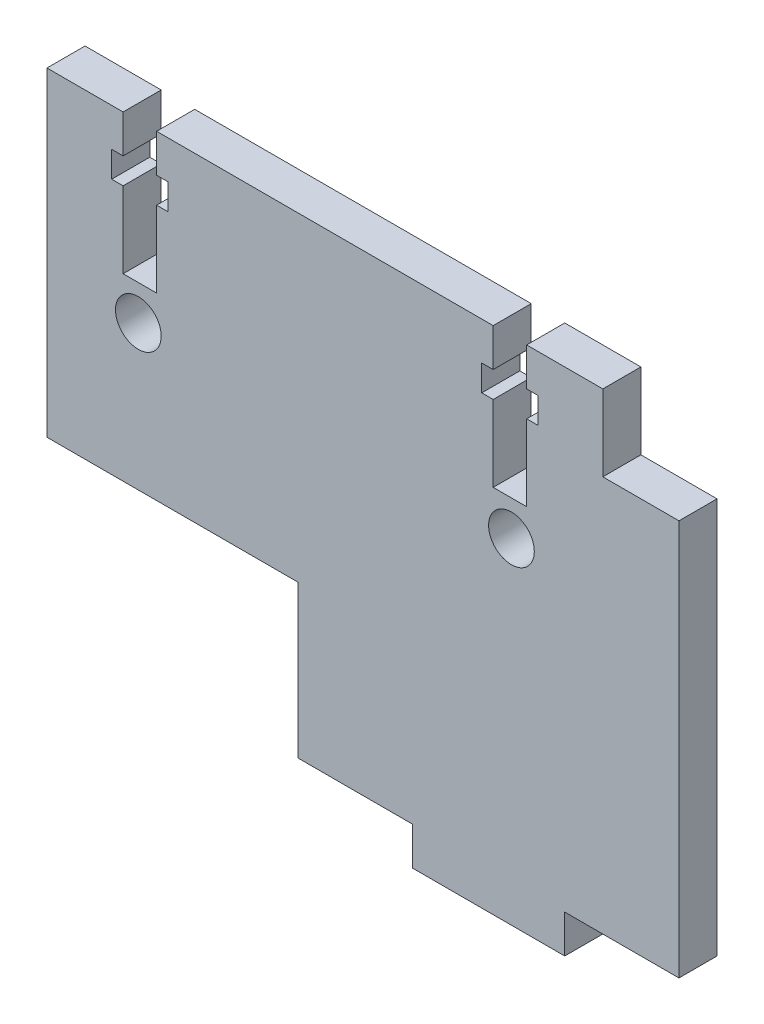
SolidWorks part; units mm, degrees
ref_plane "Front Plane" through (0, 0, 0) normal (0, 0, 1) x (1, 0, 0)
ref_plane "Top Plane" through (0, 0, 0) normal (0, 1, 0) x (1, 0, 0)
ref_plane "Right Plane" through (0, 0, 0) normal (1, 0, 0) x (0, 0, -1)
sketch "Sketch1" plane through (0, 0, 0) normal (0, 0, 1) x (1, 0, 0)
  line L0 (26.5, -31) -> (26.5, -36)
  line L1 (-41.5, 31) -> (41.5, 31)
  line L2 (-41.5, 31) -> (-41.5, -31)
  line L3 (-41.5, -31) -> (6.5, -31)
  line L4 (41.5, 31) -> (41.5, -31)
  line L5 (26.5, -36) -> (6.5, -36)
  line L6 (6.5, -36) -> (6.5, -31)
  line L7 (26.5, -31) -> (41.5, -31)
  dimension "D1" = 83
  dimension "D2" = 62
  dimension "D3" = 31
  dimension "D4" = 41.5
  dimension "D5" = 20
  dimension "D6" = 15
  dimension "D7" = 5
extrude "Boss-Extrude1" add sketch "Sketch1" along normal blind 5
sketch "Sketch2" plane through (0, 0, 0) normal (0, 0, -1) x (-1, 0, 0)
  line L1 (41.5, -31) -> (8.5, -31)
  line L2 (41.5, -31) -> (41.5, -11)
  line L3 (41.5, -11) -> (8.5, -11)
  line L4 (8.5, -31) -> (8.5, -11)
  line L5 (-41.5, 31) -> (-31.5, 31)
  line L6 (-41.5, 31) -> (-41.5, 21)
  line L7 (-41.5, 21) -> (-31.5, 21)
  line L8 (-31.5, 31) -> (-31.5, 21)
  dimension "D1" = 33
  dimension "D2" = 20
  dimension "D3" = 10
  dimension "D4" = 10
extrude "Cut-Extrude1" cut sketch "Sketch2" against normal blind 5
sketch "Sketch3" plane through (0, 0, 0) normal (0, 0, -1) x (-1, 0, 0)
  line L0 (29.3, 10.8) -> (29.3, 25.6452) construction
  line L1 (31.5, 22.6) -> (31.5, 12.6)
  line L2 (27.1, 26) -> (27.1, 31)
  line L3 (33, 26) -> (31.5, 26)
  line L4 (33, 22.6) -> (33, 26)
  line L5 (31.5, 22.6) -> (33, 22.6)
  line L6 (25.6, 26) -> (27.1, 26)
  line L7 (25.6, 22.6) -> (25.6, 26)
  line L8 (27.1, 22.6) -> (25.6, 22.6)
  line L9 (27.1, 12.6) -> (31.5, 12.6)
  line L10 (31.5, 31) -> (31.5, 26)
  line L11 (27.1, 31) -> (31.5, 31)
  line L12 (27.1, 12.6) -> (27.1, 22.6)
  line L13 (-31.5, 31) -> (41.5, 31) construction
  line L14 (41.5, 31) -> (41.5, -11) construction
  line L15 (-19.3, 10.8) -> (-19.3, 25.6452) construction
  line L16 (-17.1, 22.6) -> (-17.1, 12.6)
  line L17 (-21.5, 26) -> (-21.5, 31)
  line L18 (-15.6, 26) -> (-17.1, 26)
  line L19 (-15.6, 22.6) -> (-15.6, 26)
  line L20 (-17.1, 22.6) -> (-15.6, 22.6)
  line L21 (-23, 26) -> (-21.5, 26)
  line L22 (-23, 22.6) -> (-23, 26)
  line L23 (-21.5, 22.6) -> (-23, 22.6)
  line L24 (-21.5, 12.6) -> (-17.1, 12.6)
  line L25 (-17.1, 31) -> (-17.1, 26)
  line L26 (-21.5, 31) -> (-17.1, 31)
  line L27 (-21.5, 12.6) -> (-21.5, 22.6)
  line L28 (-41.5, -31) -> (-41.5, 21) construction
  dimension "D1" = 5
  dimension "D2" = 3.4
  dimension "D3" = 10
  dimension "D4" = 2.2
  dimension "D5" = 4.4
  dimension "D6" = 1.5
  dimension "D7" = 1.5
  dimension "D8" = 10
  dimension "D9" = 5
  dimension "D10" = 3.4
  dimension "D11" = 10
  dimension "D12" = 2.2
  dimension "D13" = 4.4
  dimension "D14" = 1.5
  dimension "D15" = 1.5
  dimension "D16" = 20
extrude "Cut-Extrude2" cut sketch "Sketch3" against normal blind 10
sketch "Sketch4" plane through (0, 0, 0) normal (0, 0, -1) x (-1, 0, 0)
  line L0 (-17.1, 31) -> (27.1, 31) construction
  line L1 (41.5, 31) -> (41.5, -11) construction
  circle A0 centre (29.5, 8) radius 3
  circle A1 centre (-19.5, 8) radius 3
  dimension "D2" = 6
  dimension "D3" = 6
  dimension "D1" = 23
  dimension "D4" = 49
  dimension "D5" = 12
extrude "Cut-Extrude3" cut sketch "Sketch4" against normal blind 10
